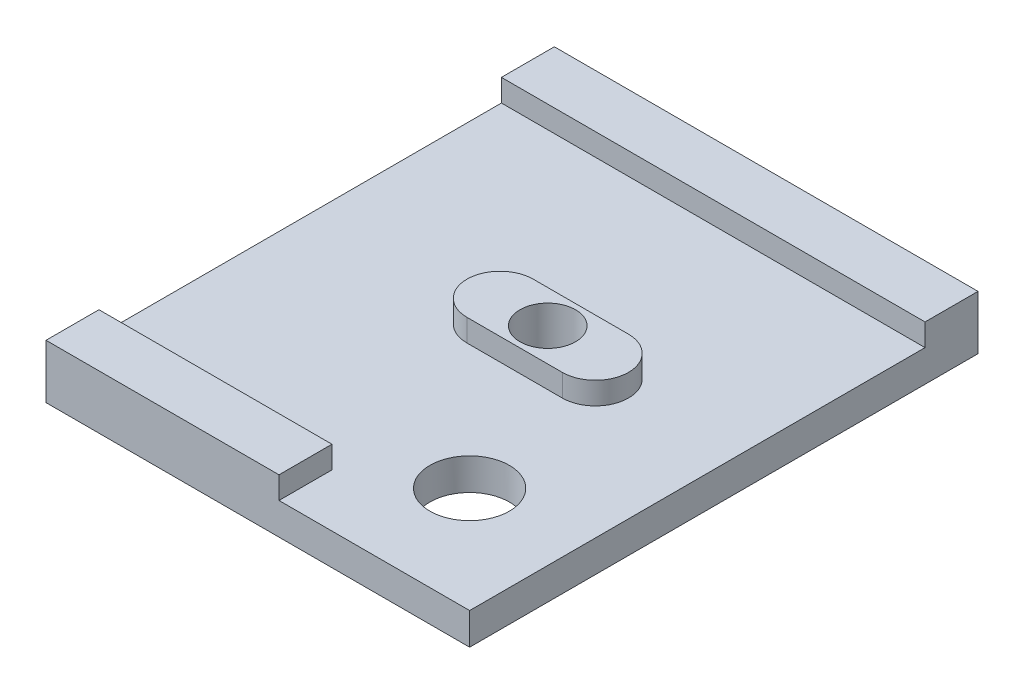
SolidWorks part; units mm, degrees
ref_plane "Front Plane" through (0, 0, 0) normal (0, 0, 1) x (1, 0, 0)
ref_plane "Top Plane" through (0, 0, 0) normal (0, 1, 0) x (1, 0, 0)
ref_plane "Right Plane" through (0, 0, 0) normal (1, 0, 0) x (0, 0, -1)
sketch "Sketch2" plane through (0, 0, 0) normal (0, 1, 0) x (1, 0, 0)
  line L0 (-221.3858, 0) -> (10847.9046, 0) construction
  line L1 (0, -221.3858) -> (0, 10847.9046) construction
  line L3 (-20, -24) -> (20, -24)
  line L4 (-20, -24) -> (-20, 24)
  line L5 (-20, 24) -> (20, 24)
  line L6 (20, -24) -> (20, 24)
  line L7 (-20, -24) -> (20, 24) construction
  line L8 (-20, 24) -> (20, -24) construction
  point P4 (0, 0)
  dimension "D1" = 40
  dimension "D2" = 48
extrude "Boss-Extrude3" add sketch "Sketch2" along normal blind 3
sketch "Sketch3" plane through (0, 3, 0) normal (0, 1, 0) x (1, 0, 0)
  line L0 (20, -24) -> (20, 24) construction
  line L1 (-2, 4) -> (7, 4)
  line L2 (-2, 4) -> (-2, -2.25)
  line L3 (-2, -2.25) -> (7, -2.25)
  line L4 (7, 4) -> (7, -2.25)
  line L5 (-2, 4) -> (7, -2.25) construction
  line L6 (-2, -2.25) -> (7, 4) construction
  line L7 (20, 24) -> (-20, 24) construction
  line L8 (-20, 24) -> (-20, -24) construction
  line L9 (-20, 24) -> (20, 24)
  line L10 (-20, 24) -> (-20, 19)
  line L11 (-20, 19) -> (20, 19)
  line L12 (20, 24) -> (20, 19)
  line L13 (-20, -19) -> (2, -19)
  line L14 (-20, -19) -> (-20, -24)
  line L15 (-20, -24) -> (2, -24)
  line L16 (2, -19) -> (2, -24)
  line L17 (-20, -24) -> (20, -24) construction
  circle A0 centre (7, 0.875) radius 3.125
  circle A2 centre (-2, 0.875) radius 3.125
  point P0 (2.5, 0.875)
  line M7 (20, -24) -> (20, 24)
  line M8 (20, 24) -> (-20, 24)
  line M9 (-20, 24) -> (-20, -24)
  line M10 (-20, -24) -> (20, -24)
  dimension "D1" = 13
  dimension "D2" = 9
  dimension "D3" = 6.25
  dimension "D4" = 20
  dimension "D5" = 5
  dimension "D6" = 5
  dimension "D7" = 18
extrude "Boss-Extrude4" add sketch "Sketch3" along normal blind 2.1 contours L16 L13 M9 M10 | L2 A2 | L4 A0 | A2 L3 A0 L1 | L2 A2 | L4 A0 | L11 M9 M7 M8
sketch "Sketch4" plane through (0, 5.1, 0) normal (0, 1, 0) x (1, 0, 0)
  line L0 (-1005.125, 0.875) -> (48994.875, 0.875) construction
  line L1 (2.5, -996) -> (2.5, 49004) construction
  line L2 (-2, 4) -> (7, 4) construction
  arc A0 (-2, 4) -> (-2, -2.25) centre (-2, 0.875) ccw construction
  circle A1 centre (2.5, 0.875) radius 2.625
  point P6 (-5.125, 0.875)
  point P11 (2.5, 4)
  dimension "D1" = 5.25
extrude "Cut-Extrude1" cut sketch "Sketch4" against normal through all both and the other way through all
sketch "Sketch5" plane through (0, 3, 0) normal (0, 1, 0) x (1, 0, 0)
  line L0 (20, -24) -> (20, 19) construction
  line L1 (2, -24) -> (20, -24) construction
  circle A0 centre (10, -14) radius 3.75
  dimension "D1" = 7.5
  dimension "D2" = 10
  dimension "D3" = 10
extrude "Cut-Extrude2" cut sketch "Sketch5" against normal through all both and the other way through all
